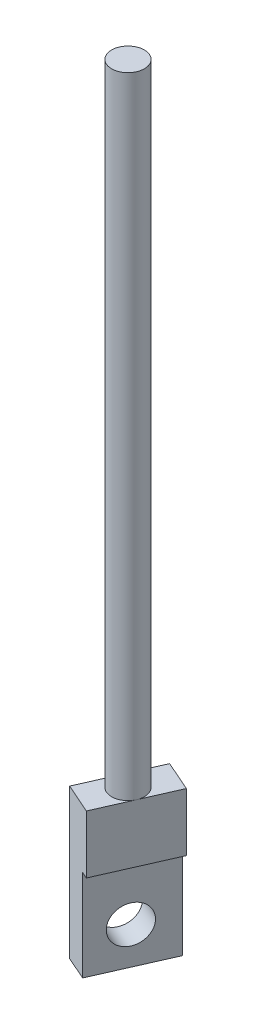
SolidWorks part; units mm, degrees
ref_plane "Front Plane" through (0, 0, 0) normal (0, 0, 1) x (1, 0, 0)
ref_plane "Top Plane" through (0, 0, 0) normal (0, 1, 0) x (1, 0, 0)
ref_plane "Right Plane" through (0, 0, 0) normal (1, 0, 0) x (0, 0, -1)
sketch "Sketch2" plane through (0, 0, 0) normal (0, 1, 0) x (1, 0, 0)
  circle A0 centre (-10.2955, 5.8266) radius 3.5
  dimension "D1" = 7
extrude "Boss-Extrude1" add sketch "Sketch2" along normal blind 135
ref_plane "Plane1" through (-7.5678, 0, -3.338) normal (-0.9149, 0, -0.4036) x (-0.4036, 0, 0.9149)
sketch "Sketch3" plane through (-7.5678, 0, -3.338) normal (-0.9149, 0, -0.4036) x (-0.4036, 0, 0.9149)
  line L0 (-9.2961, 0.0187) -> (-9.2961, -32)
  line L1 (-9.2961, -32) -> (6.9403, -32)
  line L2 (6.9403, -32) -> (6.9403, 0)
  line L3 (6.9403, 0) -> (-9.2961, 0.0187)
  line L4 (2.3239, 0) -> (2.3239, 135) construction
  line L5 (-4.6761, 135) -> (-4.6761, 0) construction
  point P2 (-12.5564, 1.938)
  dimension "D1" = 4.6164
  dimension "D2" = 4.62
  dimension "D3" = 32
extrude "Boss-Extrude2" add sketch "Sketch3" along normal blind 7
sketch "Sketch4" plane through (-7.5678, 0, -3.338) normal (0.9149, 0, 0.4036) x (0.4036, 0, -0.9149)
  circle A0 centre (0.8946, -24.0704) radius 4
extrude "Cut-Extrude1" cut sketch "Sketch4" against normal blind 7
sketch "Sketch5" plane through (-2.8009, 0, 6.35) normal (-0.4036, 0, 0.9149) x (0.9149, 0, 0.4036)
  line L1 (-8.2713, -32) -> (-9.8354, -32)
  line L2 (-8.2713, -32) -> (-8.2713, -12.4266)
  line L3 (-8.2713, -12.4266) -> (-9.8354, -12.4266)
  line L4 (-9.8354, -32) -> (-9.8354, -12.4266)
extrude "Cut-Extrude2" cut sketch "Sketch5" against normal through all
